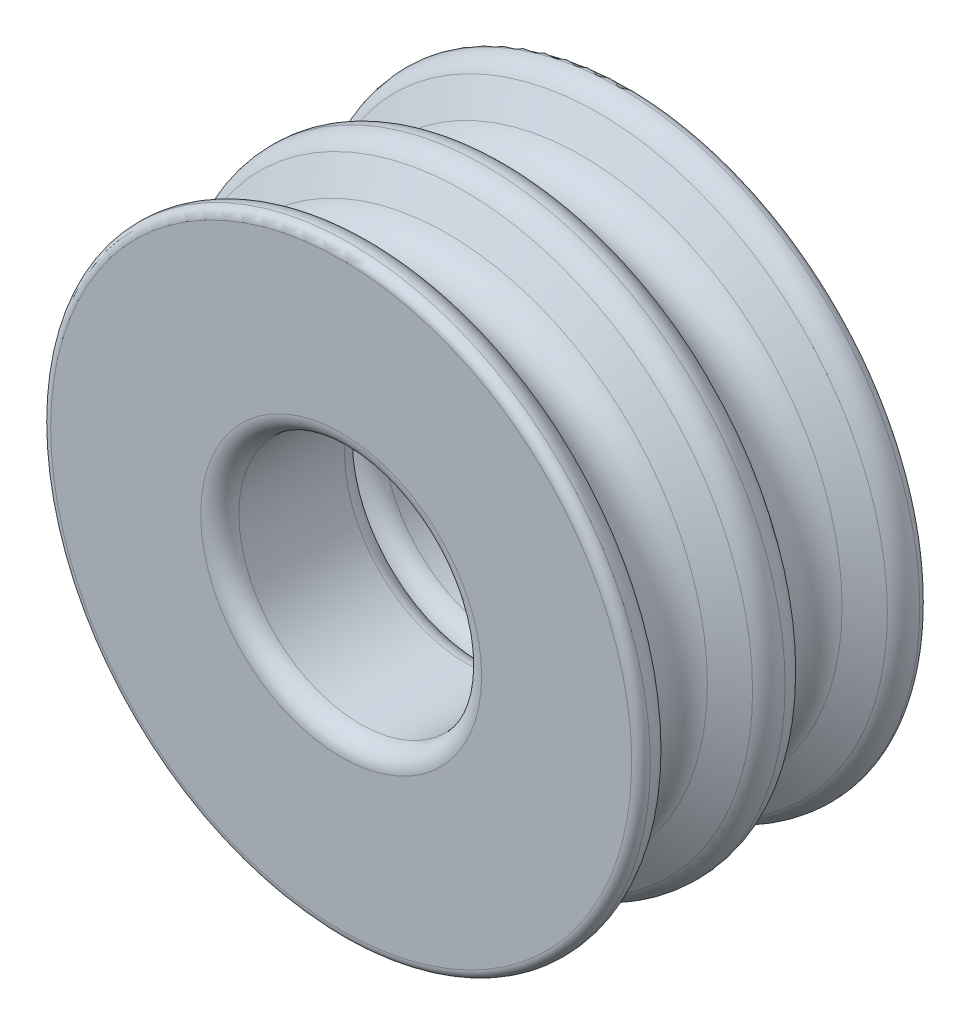
SolidWorks part; units mm, degrees
ref_plane "Front Plane" through (0, 0, 0) normal (0, 0, 1) x (1, 0, 0)
ref_plane "Top Plane" through (0, 0, 0) normal (0, 1, 0) x (1, 0, 0)
ref_plane "Right Plane" through (0, 0, 0) normal (1, 0, 0) x (0, 0, -1)
sketch "Sketch1" plane through (0, 0, 0) normal (1, 0, 0) x (0, 0, -1)
  line L0 (0, 0) -> (0, 17451.5356) construction
  line L2 (-4, 0) -> (-4, 15.2006)
  line L6 (-2.4257, 15.1015) -> (-1.5588, 13.6)
  line L7 (2.4257, 15.1015) -> (1.5588, 13.6)
  line L9 (0, 0) -> (-50000, 0) construction
  line L10 (-4, 0) -> (3.525, 0)
  line L11 (3.525, 15.7) -> (3.525, 0)
  arc A0 (-4, 15.2006) -> (-3.525, 15.7) centre (-3.5, 15.2006) cw
  arc A2 (-3.525, 15.7) -> (-2.4257, 15.1015) centre (-3.465, 14.5015) cw
  arc A3 (3.525, 15.7) -> (2.4257, 15.1015) centre (3.465, 14.5015) ccw
  arc A4 (-1.5588, 13.6) -> (1.5588, 13.6) centre (0, 14.5) ccw
  point P6 (0, 0)
  point P18 (0, 12.7)
  dimension "D2" = 0.5
  dimension "D4" = 1.2
  dimension "D5" = 1.8
  dimension "D1" = 4
  dimension "D6" = 3
  dimension "D7" = 60
  dimension "D8" = 12.7
revolve "Revolve1" add sketch "Sketch1" angle 360 about L9
sketch "Sketch2" plane through (0, 0, 4) normal (0, 0, 1) x (1, 0, 0)
  circle A0 centre (0, 0) radius 6.35
  point P1 (0.3209, -5.0008)
  dimension "D2" = 12.7
extrude "Cut-Extrude1" cut sketch "Sketch2" against normal through all
fillet "Fillet1" radius 1 2 edges at (6.35, 0, -3.525) (6.35, 0, 4)
ref_plane "Plane1" through (0, 0, -3.525) normal (0, 0, -1) x (-1, 0, 0)
mirror "Mirror1" about plane through (0, 0, -3.525) normal (0, 0, -1) of bodies 109
ref_plane "Plane2" through (0, 0, 4) normal (0, 0, 1) x (1, 0, 0)
